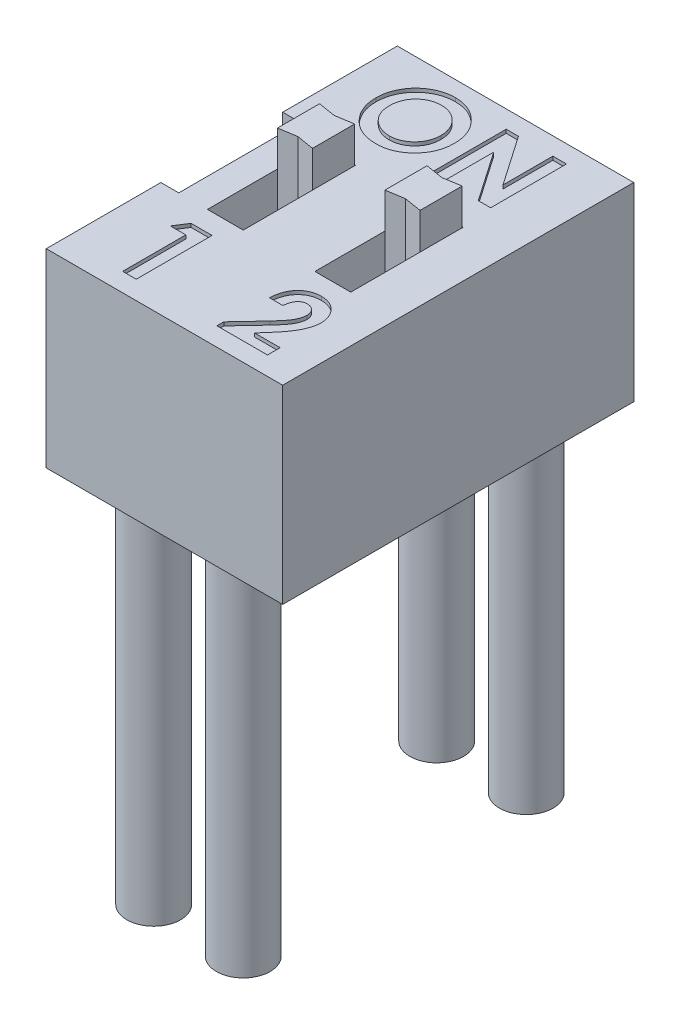
SolidWorks part; units mm, degrees
ref_plane "Front" through (0, 0, 0) normal (0, 0, 1) x (1, 0, 0)
ref_plane "Top" through (0, 0, 0) normal (0, 1, 0) x (1, 0, 0)
ref_plane "Right" through (0, 0, 0) normal (1, 0, 0) x (0, 0, -1)
sketch "Sketch1" plane through (0, 0, 0) normal (0, 1, 0) x (1, 0, 0)
  line L0 (-3.3, 1.7) -> (-3.3, 4.9)
  line L1 (-3.3, -4.9) -> (3.3, -4.9)
  line L2 (-3.3, -4.9) -> (-3.3, -1.7)
  line L3 (-3.3, 4.9) -> (3.3, 4.9)
  line L4 (3.3, -4.9) -> (3.3, 4.9)
  line L5 (-3.3, -4.9) -> (3.3, 4.9) construction
  line L6 (-3.3, 4.9) -> (3.3, -4.9) construction
  line L7 (-3.3, 1.7) -> (-2.8, 1.7)
  line L9 (-3.3, -1.7) -> (-2.8, -1.7)
  line L10 (-2.8, 1.7) -> (-2.8, -1.7)
  point P0 (0, 0)
  dimension "D1" = 6.6
  dimension "D2" = 9.8
  dimension "D3" = 3.4
  dimension "D4" = 1.7
  dimension "D5" = 0.5
extrude "Boss-Extrude1" add sketch "Sketch1" along normal blind 5.3
sketch "Sketch2" plane through (0, 5.3, 0) normal (0, 1, 0) x (1, 0, 0)
  line L1 (-2, 1.44) -> (-1, 1.44)
  line L2 (-2, 1.44) -> (-2, -1.7)
  line L3 (-2, -1.7) -> (-1, -1.7)
  line L4 (-1, 1.44) -> (-1, -1.7)
  line L5 (1, 1.44) -> (2, 1.44)
  line L6 (1, 1.44) -> (1, -1.7)
  line L7 (1, -1.7) -> (2, -1.7)
  line L8 (2, 1.44) -> (2, -1.7)
  dimension "D1" = 3.14
  dimension "D2" = 3.14
  dimension "D3" = 1.7
  dimension "D4" = 1.7
  dimension "D5" = 4
  dimension "D6" = 1
  dimension "D7" = 1
  dimension "D8" = 1
extrude "Cut-Extrude1" cut sketch "Sketch2" against normal blind 1
sketch "Sketch3" plane through (0, 4.3, 0) normal (0, 1, 0) x (1, 0, 0)
  line L0 (-1.99, 1.42) -> (-1.99, 0.2435)
  line L1 (-1.99, 0.2435) -> (-1.5, 0.3235)
  line L2 (-1.5, 0.3235) -> (-1.01, 0.2435)
  line L3 (-1.01, 0.2435) -> (-1.01, 1.42)
  line L4 (-1.01, 1.42) -> (-1.5, 1.34)
  line L5 (-1.5, 1.34) -> (-1.99, 1.42)
  line L6 (-2, 1.44) -> (-2, -1.7) construction
  line L7 (-1, -1.7) -> (-1, 1.44) construction
  line L8 (-1, -1.7) -> (-1, 1.44) construction
  line L9 (-1, 1.44) -> (-2, 1.44) construction
  line L10 (-1, 1.44) -> (-2, 1.44) construction
  line L11 (0, 1.4773) -> (0, 0) construction
  line L12 (1.5, 1.34) -> (1.99, 1.42)
  line L13 (1.01, 1.42) -> (1.5, 1.34)
  line L14 (1.01, 0.2435) -> (1.01, 1.42)
  line L15 (1.5, 0.3235) -> (1.01, 0.2435)
  line L16 (1.99, 0.2435) -> (1.5, 0.3235)
  line L17 (1.99, 1.42) -> (1.99, 0.2435)
  dimension "D1" = 0.01
  dimension "D2" = 0.01
  dimension "D3" = 0.5
  dimension "D4" = 0.5
  dimension "D5" = 0.02
  dimension "D6" = 0.02
  dimension "D7" = 0.1
extrude "Boss-Extrude2" add sketch "Sketch3" along normal blind 2
sketch "Sketch4" plane through (-2.8, 0, 0) normal (-1, 0, 0) x (0, 0, 1)
  line L0 (1.7, 5.3) -> (1.7, 0) construction
  line L1 (1.7, 2) -> (-1.7, 2)
  line L2 (1.7, 2) -> (1.7, 0)
  line L3 (1.7, 0) -> (-1.7, 0)
  line L4 (-1.7, 2) -> (-1.7, 0)
  dimension "D1" = 2
extrude "Boss-Extrude3" add sketch "Sketch4" along normal up to vertex (0.5 mm away)
sketch "Sketch5" plane through (0, 5.3, 0) normal (0, 1, 0) x (1, 0, 0)
  text T0 "ON" font "Century Gothic" height in points 8
  text T1 "1  2" font "Century Gothic" height in points 8
extrude "Cut-Extrude2" cut sketch "Sketch5" against normal blind 0.1
sketch "Sketch6" plane through (0, 0, 0) normal (0, -1, 0) x (1, 0, 0)
  line L0 (0, 4.9) -> (0, -4.9) construction
  line L1 (-1.5, 4) -> (-1, 4)
  line L2 (-1.5, 4) -> (-1.5, 3.9)
  line L3 (-1.5, 3.9) -> (-1, 3.9)
  line L4 (-1, 4) -> (-1, 3.9)
  line L5 (-3.3, 4.9) -> (3.3, 4.9) construction
  line L6 (3.3, -4.9) -> (-3.3, -4.9) construction
  line L7 (-3.3, 0) -> (3.3, 0) construction
  line L8 (-3.3, -4.9) -> (-3.3, 4.9) construction
  line L9 (3.3, 4.9) -> (3.3, -4.9) construction
  line L10 (1, 4) -> (1, 3.9)
  line L11 (1.5, 3.9) -> (1, 3.9)
  line L12 (1.5, 4) -> (1.5, 3.9)
  line L13 (1.5, 4) -> (1, 4)
  line L14 (-1.5, 4) -> (-1, 4)
  line L15 (-1.5, 4) -> (-1.5, 3.9)
  line L16 (-1.5, 3.9) -> (-1, 3.9)
  line L17 (-1, 4) -> (-1, 3.9)
  line L18 (1, 4) -> (1, 3.9)
  line L19 (1.5, 3.9) -> (1, 3.9)
  line L20 (1.5, 4) -> (1.5, 3.9)
  line L21 (1.5, 4) -> (1, 4)
  line L22 (1.5, -4) -> (1, -4)
  line L23 (1.5, -4) -> (1.5, -3.9)
  line L24 (1.5, -3.9) -> (1, -3.9)
  line L25 (1, -4) -> (1, -3.9)
  line L26 (-1, -4) -> (-1, -3.9)
  line L27 (-1.5, -3.9) -> (-1, -3.9)
  line L28 (-1.5, -4) -> (-1.5, -3.9)
  line L29 (-1.5, -4) -> (-1, -4)
  line L30 (1.5, -4) -> (1, -4)
  line L31 (1.5, -4) -> (1.5, -3.9)
  line L32 (1.5, -3.9) -> (1, -3.9)
  line L33 (1, -4) -> (1, -3.9)
  line L34 (-1, -4) -> (-1, -3.9)
  line L35 (-1.5, -3.9) -> (-1, -3.9)
  line L36 (-1.5, -4) -> (-1.5, -3.9)
  line L37 (-1.5, -4) -> (-1, -4)
  dimension "D1" = 0.1
  dimension "D2" = 0.5
  dimension "D3" = 1.5
  dimension "D4" = 4
extrude "Boss-Extrude4" add sketch "Sketch6" along normal blind 3.5 contours L4 L1 L2 L3 | L12 L13 L10 L11 | L28 L29 L26 L27 | L25 L22 L23 L24
sketch "Sketch7" plane through (0, 0, 0) normal (0, -1, 0) x (1, 0, 0)
  circle A0 centre (-1.25, 3.95) radius 0.75
  circle A1 centre (1.25, 3.95) radius 0.75
  circle A2 centre (-1.25, -3.95) radius 0.75
  circle A3 centre (1.25, -3.95) radius 0.75
extrude "Boss-Extrude5" add sketch "Sketch7" along normal blind 10 separate body
